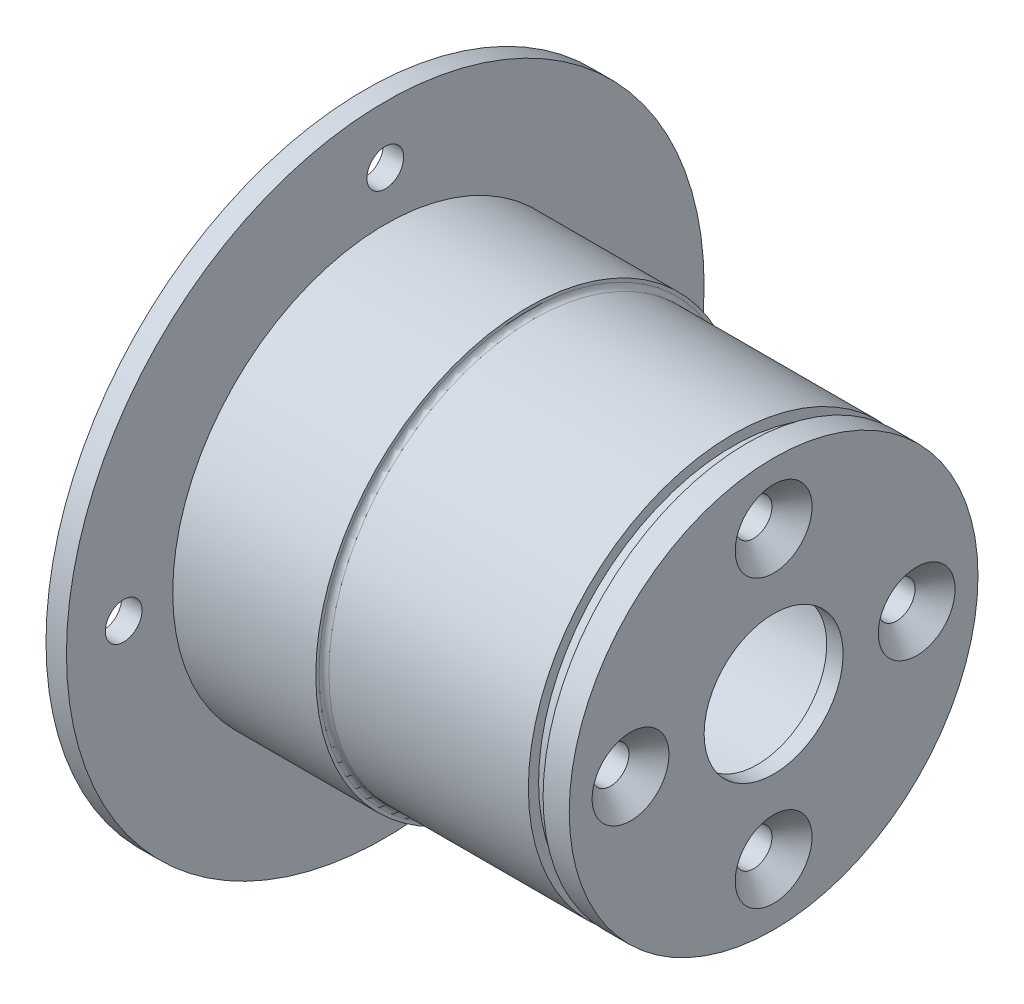
SolidWorks part; units mm, degrees
material "6061 Alloy"
ref_plane "Front Plane" through (0, 0, 0) normal (0, 0, 1) x (1, 0, 0)
ref_plane "Top Plane" through (0, 0, 0) normal (0, 1, 0) x (1, 0, 0)
ref_plane "Right Plane" through (0, 0, 0) normal (1, 0, 0) x (0, 0, -1)
sketch "Sketch2" plane through (0, 0, 0) normal (0, 0, 1) x (1, 0, 0)
  line L0 (-64.1034, 0) -> (113.4236, 0) construction
  line L2 (0, 21) -> (35, 21)
  line L3 (0, -55) -> (0, 55) construction
  line L13 (35, 21) -> (35, 12.5)
  line L14 (35, 12.5) -> (48, 12.5)
  line L19 (20, 25) -> (20, 26)
  line L21 (0, 26) -> (0, 21)
  line L25 (50, 25) -> (20, 25)
  line L26 (20, 26) -> (2.5, 26)
  line L27 (2.5, 26) -> (2.5, 39)
  line L28 (2.5, 39) -> (0, 39)
  line L29 (0, 39) -> (0, 26)
  line L30 (48, 12.5) -> (48, 8.5)
  line L31 (48, 8.5) -> (50, 8.5)
  line L32 (50, 8.5) -> (50, 25)
  point P14 (41.5, 12.5)
  dimension "D1" = 21
  dimension "D2" = 35
  dimension "D3" = 12.5
  dimension "D4" = 13
  dimension "D5" = 25
  dimension "D6" = 26
  dimension "D7" = 2.5
  dimension "D8" = 39
  dimension "D9" = 20
  dimension "D10" = 8.5
  dimension "D11" = 2
revolve "Revolve1" add sketch "Sketch2" angle 360 about L0
hole_wizard "CSK for M4 Flat Head Machine Screw1" positions "Sketch7" profile "Sketch8" countersink size "M4" standard "ANSI Metric" end condition up to next
sketch "Sketch7" plane through (50, 0, 0) normal (1, 0, 0) x (0, 0, -1)
  circle A0 centre (0, 0) radius 17.5
  point P0 (0, 17.5)
  point P2 (17.5, 0)
  point P4 (0, -17.5)
  point P6 (-17.5, 0)
  dimension "D1" = 35
sketch "Sketch8" plane through (50, 17.5, 0) normal (0, 1, 0) x (0, 0, -1)
  line L0 (0, 0) -> (0, 15)
  line L1 (0, 15) -> (2.25, 15)
  line L2 (2.25, 15) -> (2.25, 2.45)
  line L3 (2.25, 2.45) -> (4.7, 0)
  line L5 (4.7, 0) -> (0, 0)
  line L6 (-2.25, 2.45) -> (-4.7, 0) construction
  line L11 (0, -6.35) -> (0, 107.95) construction
  dimension "Thru Hole Dia." = 4.5
  dimension "Thru Hole Depth" = 15
  dimension "Near C'Sink Dia." = 9.4
  dimension "Near C'Sink Angle" = 90
fillet "Fillet1" radius 0.6 1 edges at (20, 0, 25)
ref_plane "Plane1" through (45, 0, 0) normal (1, 0, 0) x (0, 0, -1)
sketch "Sketch9" plane through (45, 0, 0) normal (1, 0, 0) x (0, 0, -1)
  circle A0 centre (0, 0) radius 23.75
  circle A1 centre (0, 0) radius 25
  dimension "D1" = 47.5
  dimension "D2" = 50
extrude "Cut-Extrude1" cut sketch "Sketch9" along normal blind 1.8
hole_wizard "M4 Clearance Hole1" positions "Sketch5" profile "Sketch6" hole size "M4" standard "ANSI Metric" end condition up to next
sketch "Sketch5" plane through (0, 0, 0) normal (-1, 0, 0) x (0, 0, 1)
  circle A0 centre (0, 0) radius 32
  point P0 (0, 32)
  point P2 (0, -32)
  point P4 (32, 0)
  point P6 (-32, 0)
  dimension "D1" = 64
sketch "Sketch6" plane through (0, 32, 0) normal (0, 1, 0) x (0, 0, 1)
  line L0 (0, 0) -> (0, 2.5)
  line L1 (0, 2.5) -> (2.25, 2.5)
  line L2 (2.25, 2.5) -> (2.25, 0)
  line L5 (2.25, 0) -> (0, 0)
  line L11 (0, -6.35) -> (0, 107.95) construction
  dimension "Thru Hole Dia." = 4.5
  dimension "Thru Hole Depth" = 2.5
